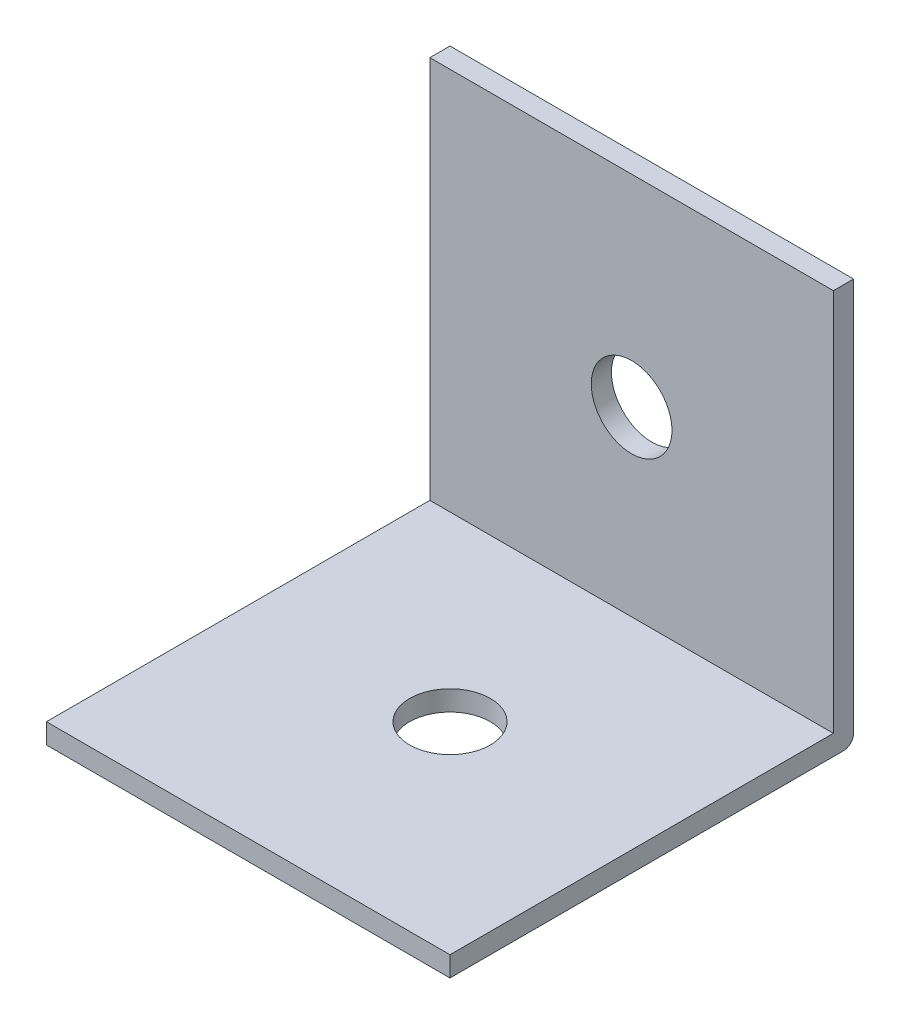
SolidWorks part; units mm, degrees
ref_plane "Front Plane" through (0, 0, 0) normal (0, 0, 1) x (1, 0, 0)
ref_plane "Top Plane" through (0, 0, 0) normal (0, 1, 0) x (1, 0, 0)
ref_plane "Right Plane" through (0, 0, 0) normal (1, 0, 0) x (0, 0, -1)
sketch "Sketch1" plane through (0, 0, 0) normal (1, 0, 0) x (0, 0, -1)
  line L1 (0, 0) -> (-20, 0)
  line L2 (0, 0) -> (0, 20)
  line L3 (0, 20) -> (-20, 20)
  line L4 (-20, 0) -> (-20, 20)
  dimension "D1" = 20
extrude "Boss-Extrude1" add sketch "Sketch1" along normal mid plane 20
sketch "Sketch3" plane through (10, 0, 0) normal (1, 0, 0) x (0, 0, -1)
  line L1 (-20, 20) -> (-1, 20)
  line L2 (-20, 20) -> (-20, 1)
  line L3 (-20, 1) -> (-1, 1)
  line L4 (-1, 20) -> (-1, 1)
  dimension "D1" = 19
extrude "Cut-Extrude1" cut sketch "Sketch3" against normal blind 20
fillet "Fillet1" radius 0.5 1 edges at (0, 0, 0)
sketch "Sketch4" plane through (0, 0, 0) normal (0, 0, -1) x (-1, 0, 0)
  line L0 (0, 0) -> (0, 10) construction
  circle A0 centre (0, 10) radius 2
  dimension "D2" = 4
  dimension "D1" = 10
extrude "Cut-Extrude2" cut sketch "Sketch4" against normal blind 2
sketch "Sketch5" plane through (0, 0, 0) normal (0, -1, 0) x (1, 0, 0)
  line L0 (0, 0) -> (0, 10) construction
  circle A0 centre (0, 10) radius 2
  dimension "D2" = 4
  dimension "D1" = 10
extrude "Cut-Extrude3" cut sketch "Sketch5" against normal blind 2
